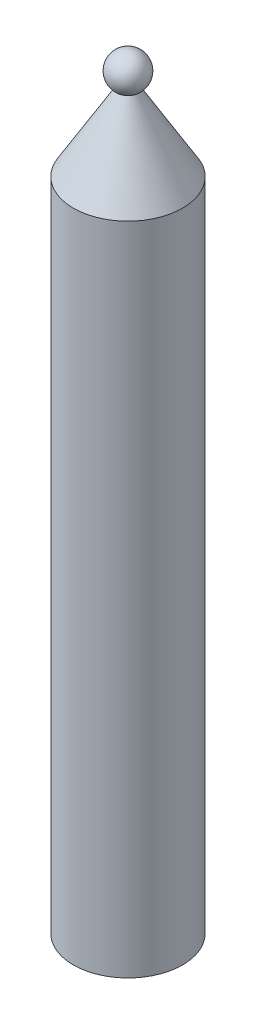
SolidWorks part; units mm, degrees
ref_plane "Front Plane" through (0, 0, 0) normal (0, 0, 1) x (1, 0, 0)
ref_plane "Top Plane" through (0, 0, 0) normal (0, 1, 0) x (1, 0, 0)
ref_plane "Right Plane" through (0, 0, 0) normal (1, 0, 0) x (0, 0, -1)
sketch "Sketch3" plane through (0, 0, 0) normal (0, 0, 1) x (1, 0, 0)
  line L0 (0, 0) -> (-10, 0)
  line L1 (-10, 0) -> (-10, 120)
  line L2 (-10, 120) -> (-1.6529, 134)
  line L3 (0, 140) -> (0, 0)
  arc A0 (-1.6529, 134) -> (0, 140) centre (0, 136.7723) cw
  dimension "D1" = 120
  dimension "D2" = 140
  dimension "D3" = 10
  dimension "D4" = 14
revolve "Revolve1" add sketch "Sketch3" angle 360 about L3
sketch "Sketch4" plane through (0, 0, 0) normal (0, 0, 1) x (1, 0, 0)
  line L0 (0, 0) -> (5, 0)
  line L1 (5, 0) -> (5, 110)
  line L2 (5, 110) -> (0, 120)
  line L3 (10, 120) -> (-10, 120) construction
  line L4 (0, 120) -> (0, 0)
  dimension "D1" = 5
  dimension "D2" = 110
revolve "Cut-Revolve1" cut sketch "Sketch4" angle 360 about L4
